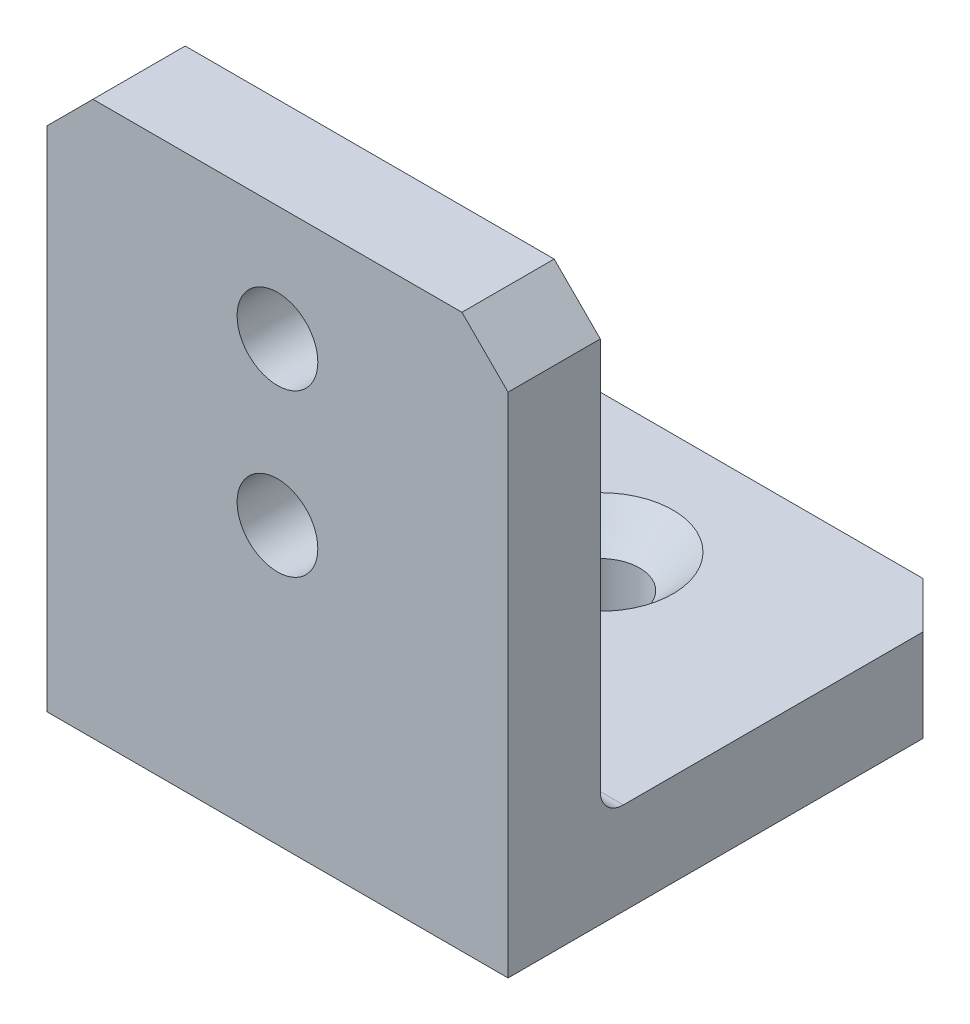
SolidWorks part; units mm, degrees
ref_plane "Piano frontale" through (0, 0, 0) normal (0, 0, 1) x (1, 0, 0)
ref_plane "Piano superiore" through (0, 0, 0) normal (0, 1, 0) x (1, 0, 0)
ref_plane "Piano destro" through (0, 0, 0) normal (1, 0, 0) x (0, 0, -1)
sketch "Schizzo1" plane through (0, 0, 0) normal (0, 0, 1) x (1, 0, 0)
  line L0 (0, 0) -> (20, 0)
  line L1 (20, 0) -> (20, 4)
  line L2 (20, 4) -> (0, 4)
  line L3 (0, 4) -> (0, 0)
  dimension "D1" = 4
  dimension "D2" = 20
extrude "Estrusione-Estrusione1" add sketch "Schizzo1" along normal blind 20
sketch "Schizzo2" plane through (0, 4, 0) normal (0, 1, 0) x (1, 0, 0)
  line L1 (0, -20) -> (20, -20)
  line L2 (0, -20) -> (0, -16)
  line L3 (0, -16) -> (20, -16)
  line L4 (20, -20) -> (20, -16)
  dimension "D1" = 4
  dimension "D2" = 20
extrude "Estrusione-Estrusione2" add sketch "Schizzo2" along normal blind 20
sketch "Schizzo7" plane through (0, 0, 16) normal (0, 0, -1) x (-1, 0, 0)
  line L0 (-10, 24) -> (-10, 4) construction
  line L1 (-20, 24) -> (0, 24) construction
  line L2 (-20, 4) -> (0, 4) construction
  circle A0 centre (-10, 19) radius 1.75
  circle A1 centre (-10, 12) radius 1.75
  dimension "D1" = 3.5
  dimension "D2" = 5
  dimension "D3" = 7
extrude "Taglio-Estrusione2" cut sketch "Schizzo7" against normal up to next
fillet "Raccordo1" radius 1 1 edges
chamfer "Smusso1" distance 2 angle 45 2 edges at (0, 24, 18) (20, 24, 18)
chamfer "Smusso3" distance 2 angle 45 2 edges at (0, 2, 0) (20, 2, 0)
sketch "Sketch1" plane through (0, 4, 0) normal (0, 1, 0) x (1, 0, 0)
  line L0 (18, 0) -> (2, 0) construction
  point P3 (10, -6)
  dimension "D1" = 6
hole_wizard "CSK for M3 Oval Head Machine Screw1" positions "3DSketch1" profile "Sketch2" countersink size "M3" standard "Ansi Metric" end condition through all
sketch3d "3DSketch1"
  point P0 (10, 4, 6)
sketch "Sketch2" plane through (10, 4, 6) normal (1, 0, 0) x (0, 0, 1)
  line L0 (0, 0) -> (0, 4)
  line L1 (0, 4) -> (1.7, 4)
  line L2 (1.7, 4) -> (1.7, 1.45)
  line L3 (1.7, 1.45) -> (3.15, 0)
  line L5 (3.15, 0) -> (0, 0)
  line L6 (-1.7, 1.45) -> (-3.15, 0) construction
  line L11 (0, -6.35) -> (0, 107.95) construction
  dimension "Thru Hole Dia." = 3.4
  dimension "Thru Hole Depth" = 4
  dimension "Near C'Sink Dia." = 6.3
  dimension "Near C'Sink Angle" = 90
